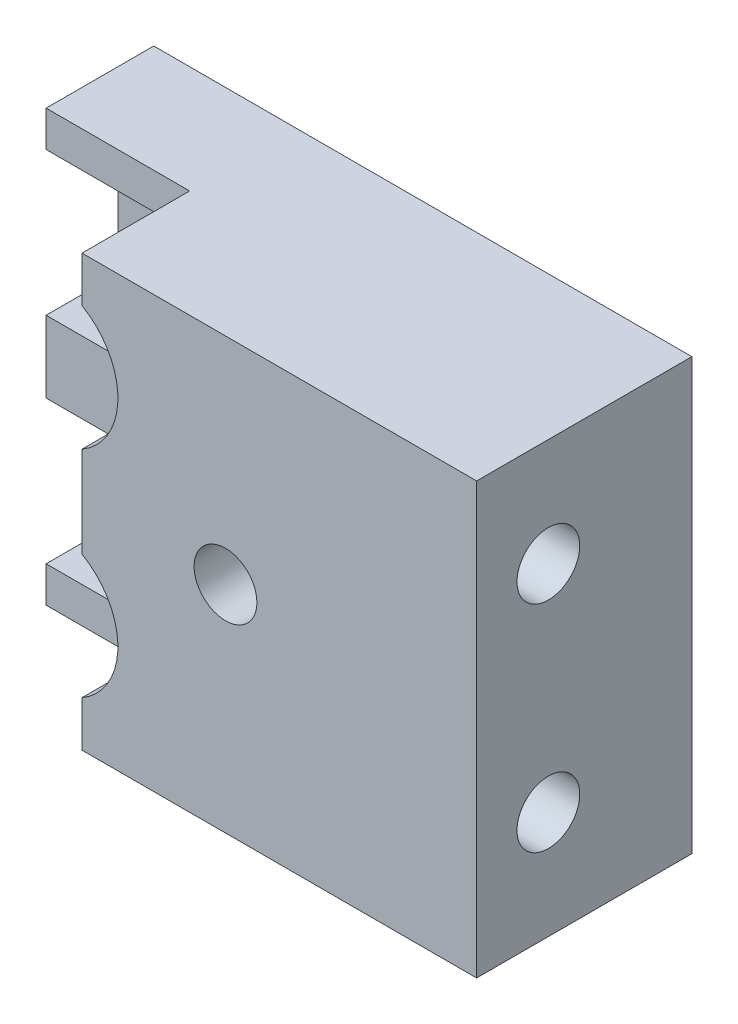
SolidWorks part; units mm, degrees
ref_plane "Front Plane" through (0, 0, 0) normal (0, 0, 1) x (1, 0, 0)
ref_plane "Top Plane" through (0, 0, 0) normal (0, 1, 0) x (1, 0, 0)
ref_plane "Right Plane" through (0, 0, 0) normal (1, 0, 0) x (0, 0, -1)
sketch "Sketch1" plane through (0, 0, 0) normal (0, 0, 1) x (1, 0, 0)
  line L1 (0, 0) -> (150, 0)
  line L2 (0, 0) -> (0, 120)
  line L3 (0, 120) -> (150, 120)
  line L4 (150, 0) -> (150, 120)
  dimension "D1" = 150
  dimension "D2" = 120
extrude "Boss-Extrude1" add sketch "Sketch1" along normal blind 60
sketch "Sketch2" plane through (0, 0, 60) normal (0, 0, 1) x (1, 0, 0)
  line L0 (0, 120) -> (0, 0) construction
  line L1 (0, 110) -> (10, 110)
  line L2 (0, 110) -> (0, 70)
  line L3 (0, 70) -> (10, 70)
  line L4 (10, 110) -> (10, 70)
  line L6 (0, 50) -> (10, 50)
  line L7 (0, 50) -> (0, 10)
  line L8 (0, 10) -> (10, 10)
  line L9 (10, 50) -> (10, 10)
  dimension "D1" = 10
  dimension "D2" = 10
  dimension "D3" = 40
  dimension "D4" = 10
  dimension "D5" = 40
  dimension "D6" = 10
extrude "Cut-Extrude1" cut sketch "Sketch2" against normal blind 60
sketch "Sketch3" plane through (0, 0, 60) normal (0, 0, 1) x (1, 0, 0)
  line L0 (10, 110) -> (30, 110)
  line L1 (10, 70) -> (10, 110)
  line L2 (10, 70) -> (30, 70)
  line L3 (10, 50) -> (10, 10)
  line L4 (10, 10) -> (30, 10)
  line L5 (10, 50) -> (30, 50)
  arc A0 (30, 110) -> (30, 70) centre (30, 90) cw
  arc A1 (30, 50) -> (30, 10) centre (30, 30) cw
  dimension "D2" = 20
  dimension "D1" = 40
  dimension "D3" = 20
  dimension "D4" = 20
  dimension "D5" = 40
  dimension "D6" = 20
extrude "Cut-Extrude2" cut sketch "Sketch3" against normal blind 40
sketch "Sketch4" plane through (0, 0, 20) normal (0, 0, 1) x (1, 0, 0)
  point P0 (30, 90)
  point P1 (30, 30)
hole_wizard "M20 Tapped Hole1" positions "3DSketch1" profile "Sketch5" tap size "M20" standard "ISO"
sketch3d "3DSketch1"
  point P0 (30, 90, 20)
  point P3 (30, 30, 20)
sketch "Sketch5" plane through (30, 90, 20) normal (1, 0, 0) x (0, -1, 0)
  line L0 (0, 0) -> (0, 72.7575)
  line L1 (0, 72.7575) -> (8.75, 67.5)
  line L2 (8.75, 67.5) -> (8.75, 0)
  line L5 (8.75, 0) -> (0, 0)
  line L10 (0, 72.7575) -> (-8.75, 67.5) construction
  line L11 (0, -6.35) -> (0, 107.95) construction
  dimension "Tap Drill Dia." = 17.5
  dimension "Tap Drill Depth" = 67.5
  dimension "Drill Angle" = 118
cosmetic thread "Hole Thread1" parameters "D1"=20, "D2"=20
cosmetic thread "Hole Thread2" parameters "D1"=20, "D2"=20
sketch "Sketch6" plane through (0, 0, 60) normal (0, 0, 1) x (1, 0, 0)
  line L0 (40, 107.3205) -> (40, 120)
  line L1 (150, 120) -> (0, 120) construction
  line L2 (40, 120) -> (150, 120)
  line L3 (150, 120) -> (150, 0)
  line L4 (150, 0) -> (40, 0)
  line L5 (0, 0) -> (150, 0) construction
  line L6 (40, 0) -> (40, 12.6795)
  line L7 (0, 70) -> (30, 70) construction
  line L8 (30, 50) -> (0, 50) construction
  line L9 (40, 72.6795) -> (40, 47.3205)
  line L10 (40, 107.3205) -> (40, 120)
  line L11 (40, 120) -> (0, 120)
  line L12 (0, 120) -> (0, 110)
  line L13 (0, 110) -> (30, 110)
  line L14 (0, 70) -> (30, 70)
  line L15 (0, 50) -> (0, 70)
  line L16 (0, 50) -> (30, 50)
  line L17 (0, 0) -> (40, 0)
  line L18 (0, 10) -> (30, 10)
  line L19 (0, 120) -> (40, 120)
  line L20 (40, 107.3205) -> (40, 120)
  arc A0 (30, 70) -> (30, 110) centre (30, 90) ccw construction
  arc A1 (30, 10) -> (30, 50) centre (30, 30) ccw construction
  arc A2 (40, 107.3205) -> (30, 70) centre (30, 90) cw
  arc A3 (40, 12.6795) -> (30, 50) centre (30, 30) ccw
  arc A4 (30, 110) -> (30, 70) centre (30, 90) cw
  arc A5 (30, 50) -> (30, 10) centre (30, 30) cw
  line M1 (0, 50) -> (30, 50)
  arc M2 (30, 50) -> (30, 10) centre (30, 30) cw
  line M3 (30, 10) -> (0, 10)
  line M4 (0, 10) -> (0, 0)
  line M5 (0, 0) -> (150, 0)
  line M7 (150, 120) -> (0, 120)
  line M8 (0, 120) -> (0, 110)
  line M9 (0, 110) -> (30, 110)
  arc M10 (30, 110) -> (30, 70) centre (30, 90) cw
  line M11 (30, 70) -> (0, 70)
  line M12 (0, 70) -> (0, 50)
  dimension "D1" = 40
  dimension "D2" = 40
  dimension "D3" = 40
extrude "Cut-Extrude4" cut sketch "Sketch6" against normal blind 30 contours L0 M10 M7 M8 M9 | L9 M10 M11 M12 M1 M2 | L6 M5 M2 M3 M4
sketch "Sketch7" plane through (0, 0, 60) normal (0, 0, 1) x (1, 0, 0)
  line L0 (40, 72.6795) -> (40, 47.3205) construction
  point P0 (80, 60)
  dimension "D1" = 40
  dimension "D2" = 10
hole_wizard "M20 Tapped Hole2" positions "3DSketch2" profile "Sketch8" tap size "M20" standard "ISO"
sketch3d "3DSketch2"
  point P0 (80, 60, 60)
sketch "Sketch8" plane through (80, 60, 60) normal (1, 0, 0) x (0, -1, 0)
  line L0 (0, 0) -> (0, 35.2575)
  line L1 (0, 35.2575) -> (8.75, 30)
  line L2 (8.75, 30) -> (8.75, 0)
  line L5 (8.75, 0) -> (0, 0)
  line L10 (0, 35.2575) -> (-8.75, 30) construction
  line L11 (0, -6.35) -> (0, 107.95) construction
  dimension "Tap Drill Dia." = 17.5
  dimension "Tap Drill Depth" = 30
  dimension "Drill Angle" = 118
cosmetic thread "Hole Thread3" parameters "D1"=30, "D2"=20
sketch "Sketch9" plane through (150, 0, 0) normal (1, 0, 0) x (0, 0, -1)
  point P0 (-40, 90)
  point P1 (-40, 30)
  dimension "D1" = 20
  dimension "D2" = 30
  dimension "D3" = 20
  dimension "D4" = 30
hole_wizard "M20 Tapped Hole3" positions "3DSketch3" profile "Sketch10" tap size "M20" standard "ISO"
sketch3d "3DSketch3"
  point P0 (150, 90, 40)
  point P3 (150, 30, 40)
sketch "Sketch10" plane through (150, 90, 40) normal (0, 1, 0) x (0, 0, -1)
  line L0 (0, 0) -> (0, 40.2575)
  line L1 (0, 40.2575) -> (8.75, 35)
  line L2 (8.75, 35) -> (8.75, 0)
  line L5 (8.75, 0) -> (0, 0)
  line L10 (0, 40.2575) -> (-8.75, 35) construction
  line L11 (0, -6.35) -> (0, 107.95) construction
  dimension "Tap Drill Dia." = 17.5
  dimension "Tap Drill Depth" = 35
  dimension "Drill Angle" = 118
cosmetic thread "Hole Thread4" parameters "D1"=35, "D2"=20
cosmetic thread "Hole Thread5" parameters "D1"=35, "D2"=20
